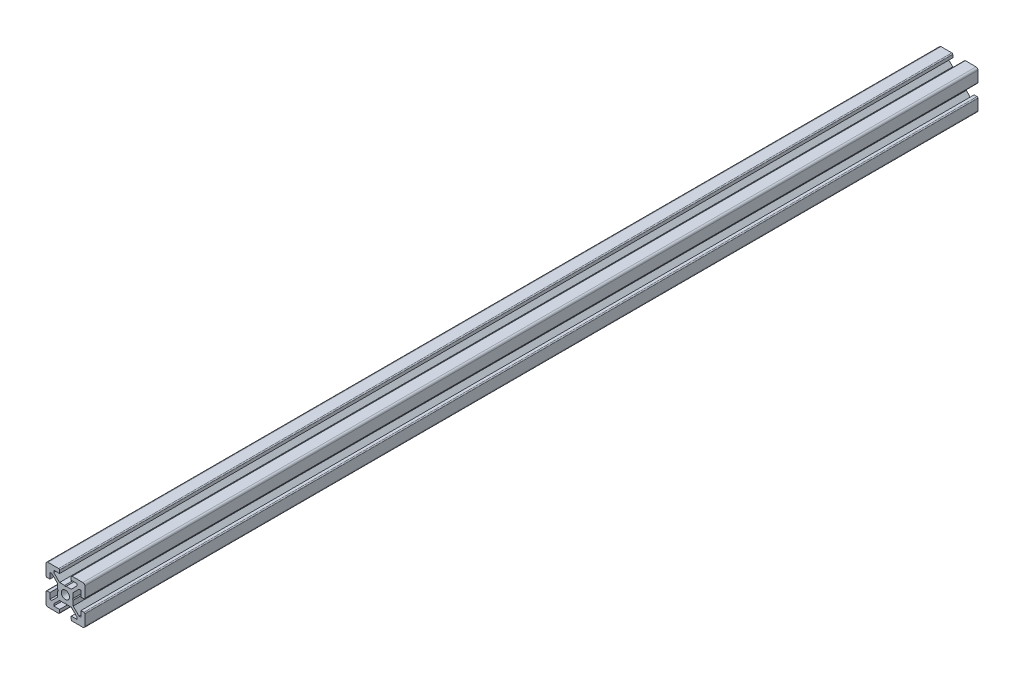
SolidWorks part; units mm, degrees
material "Lega 6061"
ref_plane "Piano frontale" through (0, 0, 0) normal (0, 0, 1) x (1, 0, 0)
ref_plane "Piano superiore" through (0, 0, 0) normal (0, 1, 0) x (1, 0, 0)
ref_plane "Piano destro" through (0, 0, 0) normal (1, 0, 0) x (0, 0, -1)
sketch "Schizzo1" plane through (0, 0, 0) normal (0, 0, 1) x (1, 0, 0)
  line L0 (0, 0) -> (-10, 0) construction
  line L1 (0, 0) -> (0, 10) construction
  line L2 (-3.6, 0) -> (-4, 0.4)
  line L3 (-4, 0.4) -> (-4, 3)
  line L4 (-4, 3) -> (-7, 6)
  line L5 (-7, 6) -> (-8, 6)
  line L6 (-8, 6) -> (-8, 3)
  line L7 (-8, 3) -> (-9.5, 3)
  line L8 (-10, 3.5) -> (-10, 9)
  line L9 (0, 0) -> (-10, 10) construction
  line L10 (0, 3.6) -> (-0.4, 4)
  line L11 (-0.4, 4) -> (-3, 4)
  line L12 (-3, 4) -> (-6, 7)
  line L13 (-6, 7) -> (-6, 8)
  line L14 (-6, 8) -> (-3, 8)
  line L15 (-3, 8) -> (-3, 9.5)
  line L16 (-3.5, 10) -> (-9, 10)
  line L17 (0, 0) -> (-10, -10) construction
  line L18 (-3.5, -10) -> (-9, -10)
  line L19 (-3, -8) -> (-3, -9.5)
  line L20 (-6, -8) -> (-3, -8)
  line L21 (-6, -7) -> (-6, -8)
  line L22 (-3, -4) -> (-6, -7)
  line L23 (-0.4, -4) -> (-3, -4)
  line L24 (0, -3.6) -> (-0.4, -4)
  line L25 (-10, -3.5) -> (-10, -9)
  line L26 (-8, -3) -> (-9.5, -3)
  line L27 (-8, -6) -> (-8, -3)
  line L28 (-7, -6) -> (-8, -6)
  line L29 (-4, -3) -> (-7, -6)
  line L30 (-4, -0.4) -> (-4, -3)
  line L31 (-3.6, 0) -> (-4, -0.4)
  line L32 (0, 0) -> (10, -10) construction
  line L33 (0, 0) -> (10, 10) construction
  line L34 (3.6, 0) -> (4, -0.4)
  line L35 (4, -0.4) -> (4, -3)
  line L36 (4, -3) -> (7, -6)
  line L37 (7, -6) -> (8, -6)
  line L38 (8, -6) -> (8, -3)
  line L39 (8, -3) -> (9.5, -3)
  line L40 (10, -3.5) -> (10, -9)
  line L41 (0, -3.6) -> (0.4, -4)
  line L42 (0.4, -4) -> (3, -4)
  line L43 (3, -4) -> (6, -7)
  line L44 (6, -7) -> (6, -8)
  line L45 (6, -8) -> (3, -8)
  line L46 (3, -8) -> (3, -9.5)
  line L47 (3.5, -10) -> (9, -10)
  line L48 (3.5, 10) -> (9, 10)
  line L49 (3, 8) -> (3, 9.5)
  line L50 (6, 8) -> (3, 8)
  line L51 (6, 7) -> (6, 8)
  line L52 (3, 4) -> (6, 7)
  line L53 (0.4, 4) -> (3, 4)
  line L54 (0, 3.6) -> (0.4, 4)
  line L55 (10, 3.5) -> (10, 9)
  line L56 (8, 3) -> (9.5, 3)
  line L57 (8, 6) -> (8, 3)
  line L58 (7, 6) -> (8, 6)
  line L59 (4, 3) -> (7, 6)
  line L60 (4, 0.4) -> (4, 3)
  line L61 (3.6, 0) -> (4, 0.4)
  arc A0 (-10, 9) -> (-9, 10) centre (-9, 9) cw
  arc A1 (-3, 9.5) -> (-3.5, 10) centre (-3.5, 9.5) ccw
  arc A2 (-9.5, 3) -> (-10, 3.5) centre (-9.5, 3.5) cw
  arc A3 (-9.5, -3) -> (-10, -3.5) centre (-9.5, -3.5) ccw
  arc A4 (-3, -9.5) -> (-3.5, -10) centre (-3.5, -9.5) cw
  arc A5 (-10, -9) -> (-9, -10) centre (-9, -9) ccw
  arc A6 (10, -9) -> (9, -10) centre (9, -9) cw
  arc A7 (3, -9.5) -> (3.5, -10) centre (3.5, -9.5) ccw
  arc A8 (9.5, -3) -> (10, -3.5) centre (9.5, -3.5) cw
  arc A9 (9.5, 3) -> (10, 3.5) centre (9.5, 3.5) ccw
  arc A10 (3, 9.5) -> (3.5, 10) centre (3.5, 9.5) cw
  arc A11 (10, 9) -> (9, 10) centre (9, 9) ccw
  circle A12 centre (0, 0) radius 2.1
  point P24 (-3, 10)
  point P27 (-10, 3)
  point P49 (-10, -3)
  point P50 (-3, -10)
  point P92 (3, -10)
  point P93 (10, -3)
  point P94 (10, 3)
  point P95 (3, 10)
  dimension "D2" = 1
  dimension "D12" = 0.5
  dimension "D13" = 4.2
  dimension "D3" = 8
  dimension "D4" = 0.4
  dimension "D5" = 45
  dimension "D6" = 6
  dimension "D7" = 12
  dimension "D8" = 20
  dimension "D9" = 2
  dimension "D10" = 4
  dimension "D11" = 45
extrude "Estrusione-Estrusione1" add sketch "Schizzo1" along normal blind 460
sketch "Schizzo2" plane through (-4, 0, 0) normal (-1, 0, 0) x (0, 0, 1)
  line L0 (460, 0) -> (0, 0) construction
  line L1 (0, -0.4) -> (0, -3) construction
  line L2 (460, -0.4) -> (460, -3) construction
  circle A0 centre (25, 0) radius 3
  circle A1 centre (435, 0) radius 3
  dimension "D1" = 6
  dimension "D2" = 25
  dimension "D3" = 25
extrude "Taglio-Estrusione1" cut sketch "Schizzo2" against normal through all
